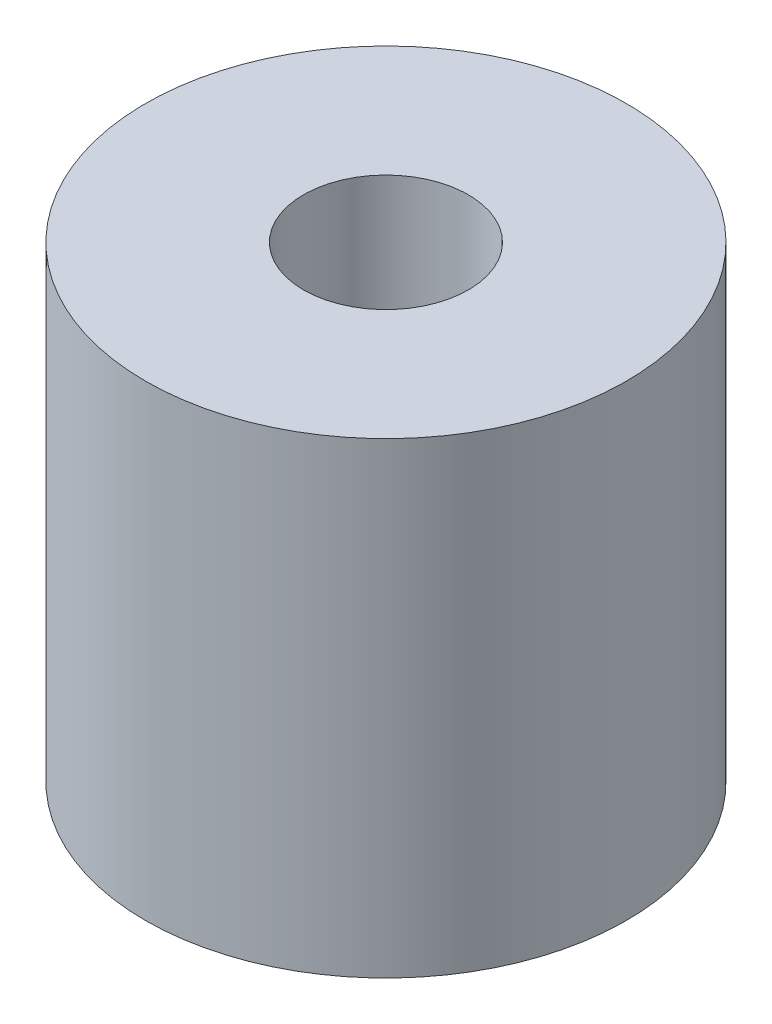
SolidWorks part; units mm, degrees
ref_plane "Front Plane" through (0, 0, 0) normal (0, 0, 1) x (1, 0, 0)
ref_plane "Top Plane" through (0, 0, 0) normal (0, 1, 0) x (1, 0, 0)
ref_plane "Right Plane" through (0, 0, 0) normal (1, 0, 0) x (0, 0, -1)
sketch "Sketch1" plane through (0, 0, 0) normal (0, 1, 0) x (1, 0, 0)
  circle A0 centre (0, 0) radius 35
  circle A1 centre (0, 0) radius 12
  dimension "D1" = 70
  dimension "D2" = 24
extrude "Boss-Extrude1" add sketch "Sketch1" along normal blind 68
